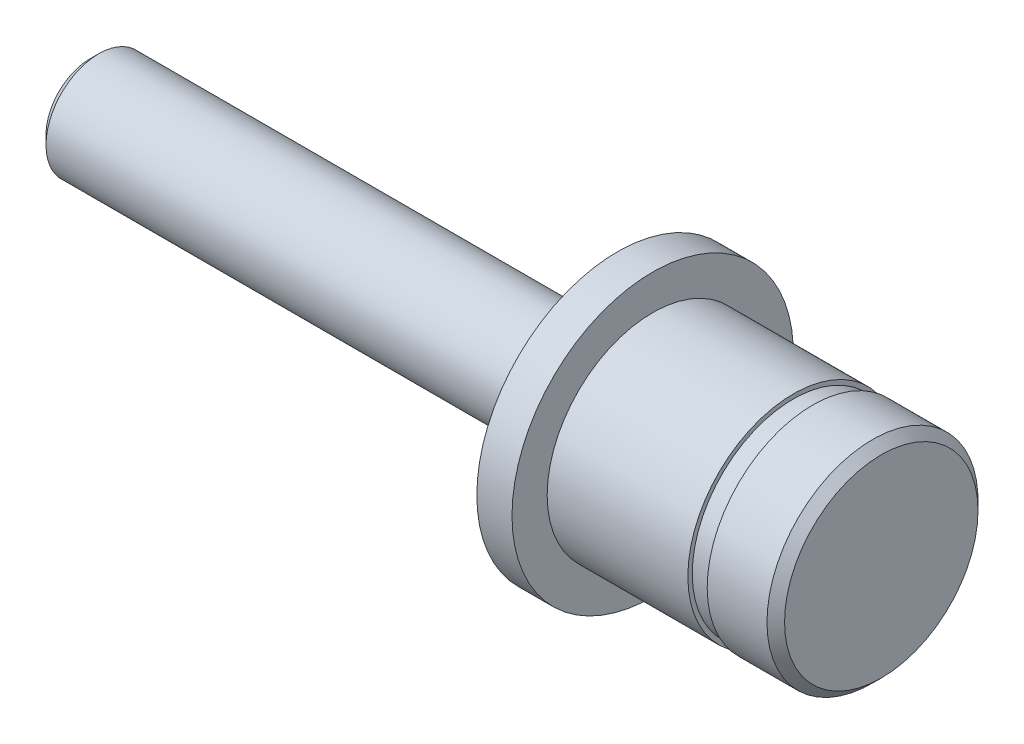
SolidWorks part; units mm, degrees
material "AISI 304"
ref_plane "Front Plane" through (0, 0, 0) normal (0, 0, 1) x (1, 0, 0)
ref_plane "Top Plane" through (0, 0, 0) normal (0, 1, 0) x (1, 0, 0)
ref_plane "Right Plane" through (0, 0, 0) normal (1, 0, 0) x (0, 0, -1)
sketch "Sketch1" plane through (0, 0, 0) normal (0, 0, 1) x (1, 0, 0)
  line L0 (-588.0669, 0) -> (28815.2785, 0) construction
  line L1 (45, 0) -> (45, 6)
  line L2 (45, 6) -> (41.1, 6)
  line L3 (41.1, 6) -> (41.1, 5.75)
  line L4 (41.1, 5.75) -> (40, 5.75)
  line L5 (40, 5.75) -> (40, 6)
  line L6 (40, 6) -> (32, 6)
  line L7 (32, 6) -> (32, 8)
  line L8 (32, 8) -> (30, 8)
  line L9 (30, 8) -> (30, 3)
  line L10 (30, 3) -> (0, 3)
  line L11 (0, 3) -> (0, 0)
  line L12 (0, 0) -> (45, 0)
  dimension "D1" = 12
  dimension "D2" = 6
  dimension "D3" = 16
  dimension "D4" = 2
  dimension "D5" = 30
  dimension "D6" = 8
  dimension "D7" = 11.5
  dimension "D8" = 1.1
  dimension "D9" = 3.9
revolve "Revolve1" add sketch "Sketch1" angle 360 about L0
cosmetic thread "Cosmetic Thread1" parameters "D1"=25, "D2"=4.891
chamfer "Chamfer1" distance 0.5 angle 45 2 edges at (45, 0, 6) (0, 0, 3)
